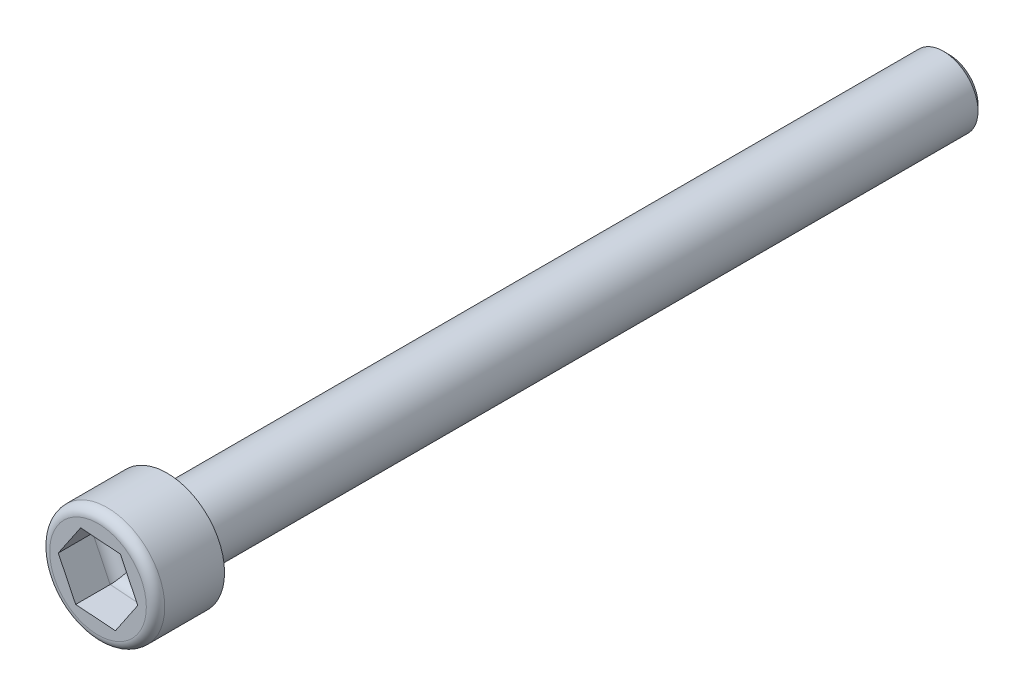
SolidWorks part; units mm, degrees
ref_plane "Ön Düzlem" through (0, 0, 0) normal (0, 0, 1) x (1, 0, 0)
ref_plane "Üst Düzlem" through (0, 0, 0) normal (0, 1, 0) x (1, 0, 0)
ref_plane "Sağ Düzlem" through (0, 0, 0) normal (1, 0, 0) x (0, 0, -1)
sketch "Sketch1" plane through (0, 0, 0) normal (0, 0, 1) x (1, 0, 0)
  circle A0 centre (0, 0) radius 1.5
  dimension "D1" = 3
extrude "Boss-Extrude1" add sketch "Sketch1" along normal blind 34
sketch "Sketch2" plane through (0, 0, 34) normal (0, 0, 1) x (1, 0, 0)
  circle A0 centre (0, 0) radius 2.5
  dimension "D1" = 5
extrude "Boss-Extrude2" add sketch "Sketch2" along normal blind 3
sketch "Sketch3" plane through (0, 0, 37) normal (0, 0, 1) x (1, 0, 0)
  line L1 (1.7276, -0.1242) -> (0.9713, 1.4341)
  line L2 (0.9713, 1.4341) -> (-0.7563, 1.5582)
  line L3 (-0.7563, 1.5582) -> (-1.7276, 0.1242)
  line L4 (-1.7276, 0.1242) -> (-0.9713, -1.4341)
  line L5 (-0.9713, -1.4341) -> (0.7563, -1.5582)
  line L6 (0.7563, -1.5582) -> (1.7276, -0.1242)
  circle A0 centre (0, 0) radius 1.5 construction
  dimension "D1" = 1.5
extrude "Cut-Extrude1" cut sketch "Sketch3" against normal blind 2
fillet "Fillet1" radius 0.4 1 edges at (2.5, 0, 37)
chamfer "Chamfer1" distance 0.25 angle 45 1 edges at (1.5, 0, 0)
fillet "Fillet2" radius 0.5 6 edges at (-0.1075, -1.4961, 35) (-1.3495, -0.655, 35) (-1.2419, 0.8412, 35) (0.1075, 1.4961, 35) (1.3495, 0.655, 35) (1.2419, -0.8412, 35)
